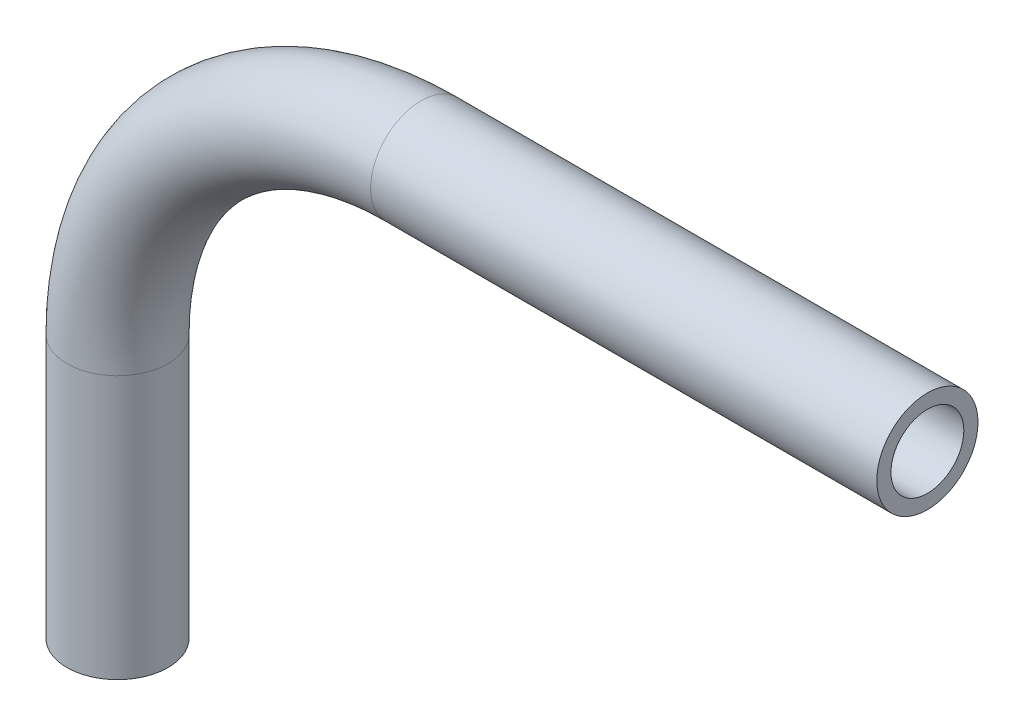
SolidWorks part; units mm, degrees
material "AISI 316 Stainless Steel Sheet (SS)"
ref_plane "Front Plane" through (0, 0, 0) normal (0, 0, 1) x (1, 0, 0)
ref_plane "Top Plane" through (0, 0, 0) normal (0, 1, 0) x (1, 0, 0)
ref_plane "Right Plane" through (0, 0, 0) normal (1, 0, 0) x (0, 0, -1)
sketch "Sketch1" plane through (0, 0, 0) normal (0, 0, 1) x (1, 0, 0)
  line L0 (0, -18.0323) -> (0, -1.5223)
  line L1 (19.05, 17.5277) -> (50.8, 17.5277)
  arc A0 (0, -1.5223) -> (19.05, 17.5277) centre (19.05, -1.5223) cw
  point P6 (0, 17.5277)
  dimension "D3" = 19.05
  dimension "D1" = 50.8
  dimension "D2" = 35.56
ref_plane "Plane1" through (50.8, 17.5277, 0) normal (1, 0, 0) x (0, 0, -1)
sketch "Sketch2" plane through (50.8, 17.5277, 0) normal (1, 0, 0) x (0, 0, -1)
  circle A0 centre (0, 0) radius 3.175
  circle A1 centre (0, 0) radius 2.286
  dimension "D1" = 6.35
  dimension "D2" = 4.572
sweep "Sweep1" add profiles "Sketch2" path "Sketch1"
